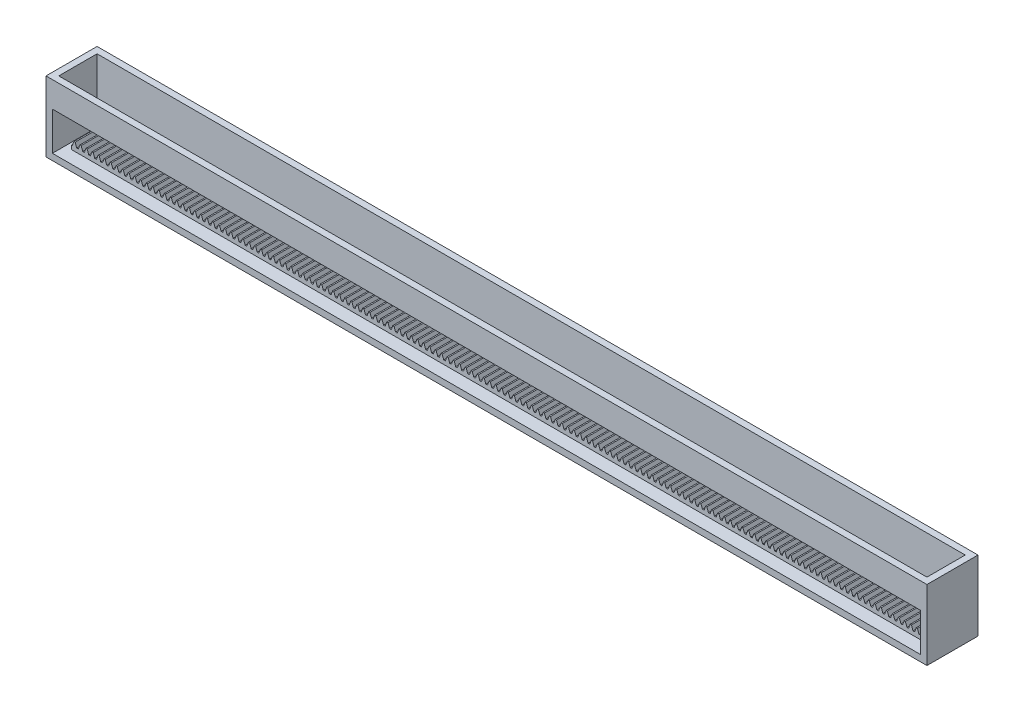
SolidWorks part; units mm, degrees
extrude "Blank" add sketch "BlankSke" against normal blind 20
sketch "BlankSke" plane through (0, 0, 0) normal (0, 0, 1) x (1, 0, 0)
  line L1 (0, 0) -> (670, 0)
  line L2 (0, 0) -> (0, 6.5)
  line L3 (0, 6.5) -> (670, 6.5)
  line L4 (670, 0) -> (670, 6.5)
  dimension "Length" = 670
  dimension "Blank_height" = 6.5
ref_plane "Plane1" through (0, 0, 0) normal (0, 0, 1) x (1, 0, 0)
ref_plane "Plane2" through (0, 0, 0) normal (0, 1, 0) x (1, 0, 0)
ref_plane "Plane3" through (0, 0, 0) normal (1, 0, 0) x (0, 0, -1)
other "Configuration Table"
sketch "HoldingSke" plane through (0, 0, 0) normal (0, 1, 0) x (1, 0, 0)
  line L0 (0, 0) -> (0.0928, 0.6602)
  line L1 (-15, 0) -> (100, 0) construction
  line L2 (0, 0) -> (-2.1039, 2.3779)
  line L3 (0, 0) -> (-11.863, 4.5341)
  line L4 (0, 0) -> (-7.1596, -4.8292)
  line L5 (0, 0) -> (-23.7986, -8.8762)
  line L6 (0, 0) -> (-10.5278, -7.1032)
  line L9 (-71.009, 38.7566) -> (868.6837, 380.7768)
  line L10 (-76.2, 3.8779) -> (-71.2, 3.8779)
  line L11 (0, 0) -> (-20, 0)
  line L12 (-76.2, 101.6) -> (-76.147, 101.6)
  line L13 (24.9733, 27.94) -> (52.9518, 28.4284)
  line L14 (24.9733, 27.94) -> (24.9743, 27.94)
  line L15 (24.9733, 27.94) -> (100.4006, 29.5858)
  circle A0 centre (0, 0) radius 19.05
  circle A1 centre (0, 0) radius 2.5
  circle A2 centre (0, 0) radius 12.7
  dimension "MPH" = 5
  dimension "Diameter" = 38.1
  dimension "Num_teeth" = 214
  dimension "Pitch" = 0.6667
  dimension "Show_teeth" = 998
  dimension "Thickness" = 12.7
  dimension "Ap" = 20
  dimension "Pitch_height" = 5
  dimension "Width" = 20
  dimension "Backlash" = 0.053
  dimension "Addendum_fac" = 1
  dimension "Dedendum_fac" = 1.25
  dimension "Clearance_fac" = 0.25
  dimension "Dedendum_add" = 0.001
  dimension "Length" = 1000
  dimension "Module" = 1.5
sketch "TooCutSkeIll" plane through (0, 0, 0) normal (0, 0, 1) x (1, 0, 0)
  line L0 (-1.8687, 6.4605) -> (-0.7447, 3.3724)
  line L1 (-0.3914, 3.125) -> (0.3914, 3.125)
  line L2 (0.7447, 3.3724) -> (1.8687, 6.4605)
  line L3 (670, 6.5) -> (0, 6.5) construction
  line L4 (0, 0) -> (0, 64.897) construction
  line L5 (-13.208, 5) -> (12.954, 5) construction
  line L6 (0, 0) -> (670, 0) construction
  line L7 (1.3371, 5) -> (1.3371, 48.7463) construction
  line L8 (-1.3371, 5) -> (-1.3371, 48.7463) construction
  line L9 (1.9251, 6.5) -> (1.9251, 6.5254)
  line L10 (-1.9251, 6.5) -> (-1.9251, 6.5254)
  line L11 (-1.9251, 6.5254) -> (1.9251, 6.5254)
  arc A0 (0.3914, 3.125) -> (0.7447, 3.3724) centre (0.3914, 3.501) ccw
  arc A1 (-0.7447, 3.3724) -> (-0.3914, 3.125) centre (-0.3914, 3.501) ccw
  arc A2 (1.9251, 6.5) -> (1.8687, 6.4605) centre (1.9251, 6.44) ccw
  arc A3 (-1.8687, 6.4605) -> (-1.9251, 6.5) centre (-1.9251, 6.44) ccw
  dimension "Pitch_height" = 5
  dimension "Addendum_plus" = 1.5254
  dimension "Pressure_angle" = 20
  dimension "Gap_width" = 2.6742
  dimension "Dedendum" = 1.875
extrude "ToothCutIll" [suppressed] cut sketch "TooCutSkeIll" against normal through all
sketch "TooCutSkeSim" plane through (0, 0, 0) normal (0, 0, 1) x (1, 0, 0)
  line L0 (0.6547, 3.125) -> (-0.6547, 3.125)
  line L1 (1.8923, 6.5254) -> (0.6547, 3.125)
  line L2 (0, 17.4625) -> (0, 53.467) construction
  line L3 (1.8923, 6.5254) -> (-1.8923, 6.5254)
  line L6 (-1.8923, 6.5254) -> (-0.6547, 3.125)
  line L9 (-1.3371, 5) -> (1.3371, 5) construction
  line L10 (0, 0) -> (670, 0) construction
  line L11 (1.3371, 5) -> (1.3371, 53.467) construction
  line L12 (-1.3371, 5) -> (-1.3371, 53.467) construction
  dimension "Pitch_height" = 5
  dimension "Addendum_plus" = 1.5254
  dimension "Pressure_angle" = 20
  dimension "Gap_width" = 2.6742
  dimension "Dedendum" = 1.875
extrude "ToothCutSim" cut sketch "TooCutSkeSim" against normal through all
pattern_linear "TeethCuts" count 143 spacing 4.7124 along (1, 0, 0) of "ToothCutIll", "ToothCutSim"
sketch "Sketch1" plane through (0, 0, 0) normal (0, -1, 0) x (1, 0, 0)
  line L0 (0, 0) -> (670, 0) construction
  line L1 (-10, -30) -> (680, -30)
  line L2 (-10, -30) -> (-10, 10)
  line L3 (-10, 10) -> (680, 10)
  line L4 (680, -30) -> (680, 10)
  line L5 (-10, -30) -> (680, 10) construction
  line L6 (-10, 10) -> (680, -30) construction
  line L7 (0, -20) -> (670, -20) construction
  line L8 (0, -20) -> (0, 0) construction
  line L9 (670, -20) -> (670, 0) construction
  point P0 (335, -10)
  dimension "D1" = 10
  dimension "D2" = 10
  dimension "D3" = 10
  dimension "D4" = 10
extrude "Boss-Extrude1" add sketch "Sketch1" along normal blind 5
sketch "Sketch3" plane through (0, 0, 0) normal (0, 1, 0) x (1, 0, 0)
  line L10 (-10, -10) -> (-10, 30)
  line L11 (-10, 30) -> (680, 30)
  line L12 (680, 30) -> (680, -10)
  line L13 (680, -10) -> (675, -10)
  line L14 (680, -10) -> (-10, -10) construction
  line L15 (675, -10) -> (675, 25)
  line L16 (675, 25) -> (-5, 25)
  line L17 (-5, 25) -> (-5, -10)
  line L18 (-5, -10) -> (-10, -10)
  dimension "D1" = 5
  dimension "D2" = 5
  dimension "D3" = 5
extrude "Boss-Extrude2" add sketch "Sketch3" along normal blind 50
sketch "Sketch6" plane through (-5, 0, 0) normal (1, 0, 0) x (0, 0, -1)
  line L1 (-10, 50) -> (-5, 50)
  line L2 (-10, 50) -> (-10, 30)
  line L3 (-10, 30) -> (-5, 30)
  line L4 (-5, 50) -> (-5, 30)
  dimension "D1" = 20
  dimension "D2" = 5
extrude "Boss-Extrude3" add sketch "Sketch6" along normal up to surface (680 mm away)
equation "' \"Module@HoldingSke\" = 6.35"
equation "' \"Num_teeth@HoldingSke\" = 12"
equation "' \"Ap@HoldingSke\" =  20"
equation "' \"Ap@HoldingSke\" = 20"
equation "' \"Width@HoldingSke\" = 0.25 * 25.4"
equation "' \"Show_teeth@HoldingSke\" = 500"
equation "' \"Backlash@HoldingSke\" = 0.009 * 25.4"
equation "' \"Addendum_fac@HoldingSke\" = 1.0"
equation "' \"Dedendum_fac@HoldingSke\" = 1.25"
equation "' \"Dedendum_add@HoldingSke\" = 0.00005 * 25.4"
equation "' \"Clearance_fac@HoldingSke\" = 0.25"
equation "' \"Pitch_height@HoldingSke\" = 1 * 25.4"
equation "' \"Length@HoldingSke\" = 4.71 * 25.4"
equation "\"Pitch@HoldingSke\" = 1 / \"Module@HoldingSke\""
equation "\"MPH@HoldingSke\" = \"Dedendum_fac@HoldingSke\" / \"Pitch@HoldingSke\" + 2 * \"Dedendum_add@HoldingSke\" + 0.002 * 25.4"
equation "\"MPH@HoldingSke\" = ((sgn( \"MPH@HoldingSke\" - \"Pitch_height@HoldingSke\")+1)*( \"MPH@HoldingSke\" - \"Pitch_height@HoldingSke\"))/2 + \"Pitch_height@HoldingSke\""
equation "\"Blank_height@BlankSke\" = \"Pitch_height@HoldingSke\" + \"Addendum_fac@HoldingSke\"  / \"Pitch@HoldingSke\" "
equation "\"Face_width@Blank\" = \"Width@HoldingSke\""
equation "\"Pressure_angle@TooCutSkeIll\" = \"Ap@HoldingSke\""
equation "\"Addendum_plus@TooCutSkeIll\" =  \"Addendum_fac@HoldingSke\"  / \"Pitch@HoldingSke\" + 0.001 *25.4"
equation "\"Dedendum@TooCutSkeIll\" = \"Dedendum_fac@HoldingSke\"  / \"Pitch@HoldingSke\""
equation "\"Pitch_height@TooCutSkeIll\" =  \"MPH@HoldingSke\""
equation "\"Gap_width@TooCutSkeIll\" = 3.14159265 / 2 / \"Pitch@HoldingSke\" + 6 * \"Backlash@HoldingSke\""
equation "\"Pressure_angle@TooCutSkeSim\" = \"Ap@HoldingSke\""
equation "\"Addendum_plus@TooCutSkeSim\" =  \"Addendum_fac@HoldingSke\"  / \"Pitch@HoldingSke\" + 0.001 * 25.4"
equation "\"Dedendum@TooCutSkeSim\" = \"Dedendum_fac@HoldingSke\"  / \"Pitch@HoldingSke\""
equation "\"Pitch_height@TooCutSkeSim\" =  \"MPH@HoldingSke\""
equation "\"Gap_width@TooCutSkeSim\" = 3.14159265 / 2 / \"Pitch@HoldingSke\" + 6 * \"Backlash@HoldingSke\""
equation "\"Root_fillet@TooCutSkeIll\" = \"Clearance_fac@HoldingSke\" / \"Pitch@HoldingSke\" + \"Dedendum_add@HoldingSke\""
equation "\"Break_rad@TooCutSkeIll\" = 0.02 / \"Pitch@HoldingSke\" * 2"
equation "\"Linear_pitch@TeethCuts\" = 3.14159265 / \"Pitch@HoldingSke\""
equation "\"Num_teeth@HoldingSke\" = int( ( \"Length@HoldingSke\" + 0 ) / (3.14159265 / \"Pitch@HoldingSke\")) + 0.9999  + 1"
equation " \"Num_teeth@TeethCuts\" = int( \"Show_teeth@HoldingSke\" ) + 1"
equation " \"Num_teeth@TeethCuts\" = ((sgn( \"Num_teeth@TeethCuts\" - \"Num_teeth@HoldingSke\" )-1)*( \"Num_teeth@TeethCuts\" - \"Num_teeth@HoldingSke\" ))/-2+ \"Num_teeth@HoldingSke\""
equation " \"Num_teeth@TeethCuts\" = ((sgn( \"Num_teeth@TeethCuts\" - 2.0)+1)*( \"Num_teeth@TeethCuts\" - 2.0))/2 +2.0"
